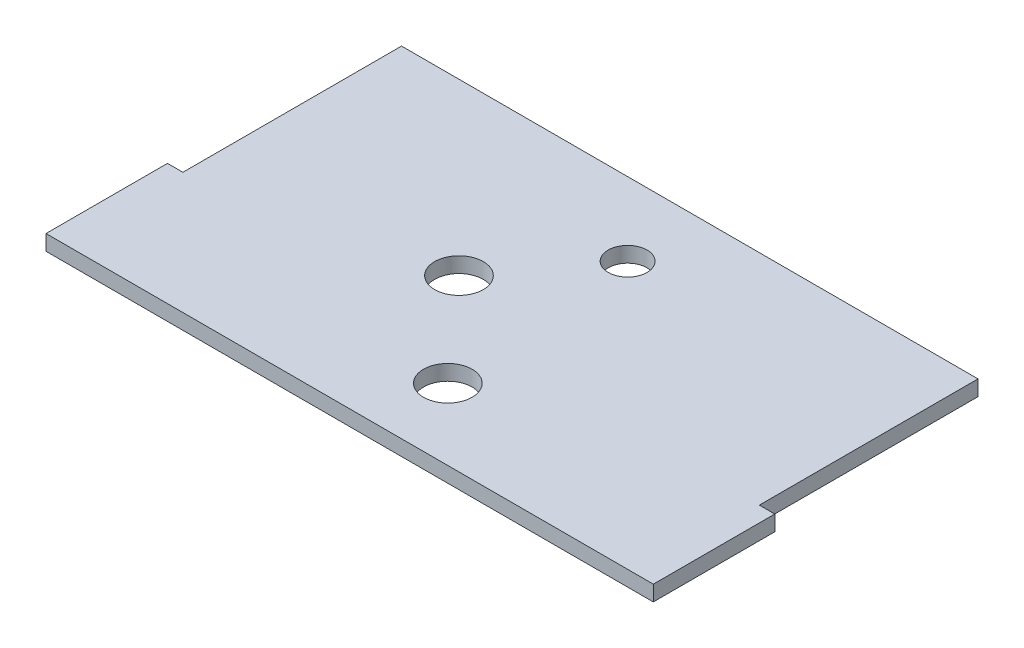
SolidWorks part; units mm, degrees
material "FiberBoard"
ref_plane "Front Plane" through (0, 0, 0) normal (0, 0, 1) x (1, 0, 0)
ref_plane "Top Plane" through (0, 0, 0) normal (0, 1, 0) x (1, 0, 0)
ref_plane "Right Plane" through (0, 0, 0) normal (1, 0, 0) x (0, 0, -1)
sketch "Sketch1" plane through (0, 0, 0) normal (0, 1, 0) x (1, 0, 0)
  line L1 (-62.5, 35) -> (62.5, 35)
  line L2 (-62.5, 35) -> (-62.5, -35)
  line L3 (-62.5, -35) -> (62.5, -35)
  line L4 (62.5, 35) -> (62.5, -35)
  line L5 (-62.5, 35) -> (62.5, -35) construction
  line L6 (-62.5, -35) -> (62.5, 35) construction
  point P0 (0, 0)
  dimension "D1" = 125
  dimension "D2" = 70
extrude "Boss-Extrude1" add sketch "Sketch1" along normal blind 3.175
hole_wizard "Ø10.0 (10) Diameter Hole1" positions "Sketch4" profile "Sketch3" hole size "Ø10.0" standard "ANSI Metric" end condition up to next
sketch "Sketch4" plane through (0, 3.175, 0) normal (0, 1, 0) x (1, 0, 0)
  line L0 (-47.5, 35) -> (22.5, -35)
  line L1 (62.5, 35) -> (-62.5, 35) construction
  line L2 (-62.5, -35) -> (62.5, -35) construction
  line L3 (6.692, -19.192) -> (5.5441, -20.3399)
  line L6 (62.5, -35) -> (62.5, 35) construction
  point P0 (-12.5, 0)
  point P3 (5.5441, -20.3399)
  dimension "D1" = 45
  dimension "D2" = 1.6234
  dimension "D3" = 27.1415
  dimension "D4" = 75
  dimension "D5" = 35
sketch "Sketch3" plane through (-12.5, 3.175, 0) normal (1, 0, 0) x (0, 0, 1)
  line L0 (0, 0) -> (0, 3.175)
  line L1 (0, 3.175) -> (5, 3.175)
  line L2 (5, 3.175) -> (5, 0)
  line L5 (5, 0) -> (0, 0)
  line L11 (0, -6.35) -> (0, 107.95) construction
  dimension "Thru Hole Dia." = 10
  dimension "Thru Hole Depth" = 3.175
hole_wizard "Ø8.0 (8) Diameter Hole1" positions "Sketch5" profile "Sketch6" hole size "Ø8.0" standard "ANSI Metric" end condition up to next
sketch "Sketch5" plane through (0, 3.175, 0) normal (0, 1, 0) x (1, 0, 0)
  line L5 (-47.5, 35) -> (22.5, -35)
  line L6 (62.5, 35) -> (-62.5, 35) construction
  line L7 (-62.5, -35) -> (62.5, -35) construction
  line L8 (2.3002, 19.9122) -> (-15.056, 2.556)
  point P0 (2.3002, 19.9122)
  point P28 (-12.5, 0)
  point P32 (-12.5, 0)
  dimension "D1" = 45
  dimension "D2" = 24.5453
  dimension "D3" = 3.6147
sketch "Sketch6" plane through (2.3002, 3.175, -19.9122) normal (1, 0, 0) x (0, 0, 1)
  line L0 (0, 0) -> (0, 3.175)
  line L1 (0, 3.175) -> (4, 3.175)
  line L2 (4, 3.175) -> (4, 0)
  line L5 (4, 0) -> (0, 0)
  line L11 (0, -6.35) -> (0, 107.95) construction
  dimension "Thru Hole Dia." = 8
  dimension "Thru Hole Depth" = 3.175
sketch "Sketch7" plane through (0, 3.175, 0) normal (0, 1, 0) x (1, 0, 0)
  line L1 (-62.5, 35) -> (-59.325, 35)
  line L2 (-62.5, 35) -> (-62.5, 10)
  line L3 (-62.5, 10) -> (-59.325, 10) construction
  line L4 (-59.325, 35) -> (-59.325, 10)
  line L5 (-62.5, -35) -> (-59.325, -35) construction
  line L6 (-62.5, -35) -> (-62.5, -10) construction
  line L7 (-62.5, -10) -> (-59.325, -10) construction
  line L8 (-59.325, -35) -> (-59.325, -10) construction
  line L9 (62.5, 35) -> (59.325, 35)
  line L10 (62.5, 35) -> (62.5, 10)
  line L11 (62.5, 10) -> (59.325, 10) construction
  line L12 (59.325, 35) -> (59.325, 10)
  line L13 (62.5, -35) -> (59.325, -35) construction
  line L14 (62.5, -35) -> (62.5, -10) construction
  line L15 (62.5, -10) -> (59.325, -10) construction
  line L16 (59.325, -35) -> (59.325, -10) construction
  line L17 (62.5, -10) -> (59.325, -10)
  line L18 (62.5, -10) -> (62.5, 10)
  line L20 (59.325, -10) -> (59.325, 10)
  line L22 (-62.5, 10) -> (-62.5, -10)
  line L23 (-62.5, -10) -> (-59.325, -10)
  line L24 (-59.325, 10) -> (-59.325, -10)
  dimension "D1" = 25
  dimension "D2" = 3.175
extrude "Cut-Extrude1" cut sketch "Sketch7" against normal through all
